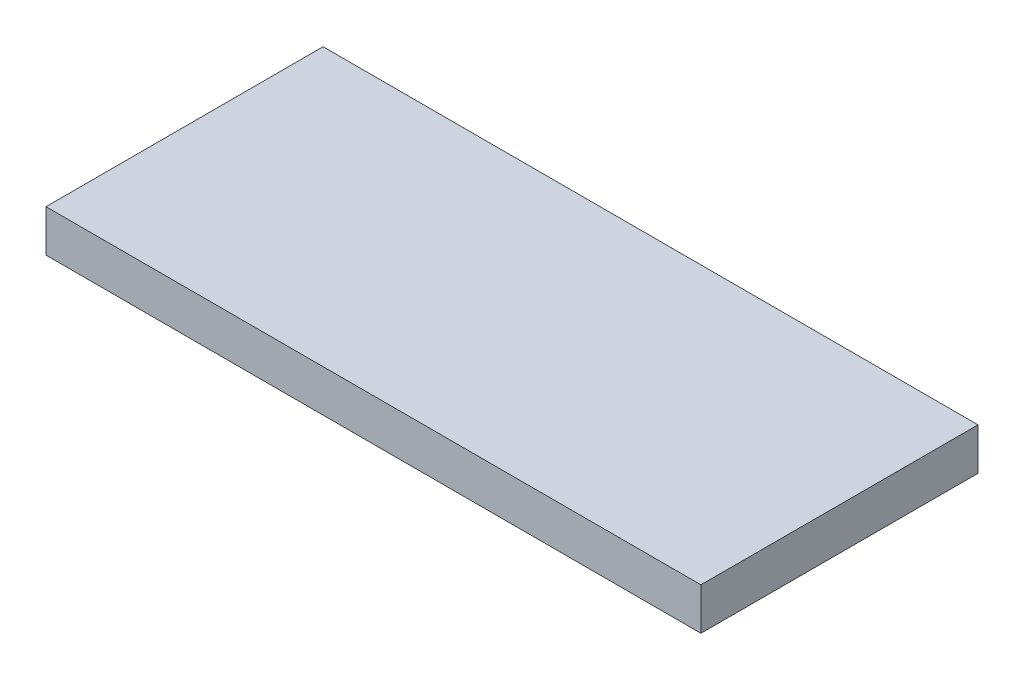
SolidWorks part; units mm, degrees
ref_plane "Спереди" through (0, 0, 0) normal (0, 0, 1) x (1, 0, 0)
ref_plane "Сверху" through (0, 0, 0) normal (0, 1, 0) x (1, 0, 0)
ref_plane "Справа" through (0, 0, 0) normal (1, 0, 0) x (0, 0, -1)
sketch "Эскиз1" plane through (0, 0, 0) normal (0, 1, 0) x (1, 0, 0)
  line L1 (0, 0) -> (78, 0)
  line L2 (0, 0) -> (0, 33)
  line L3 (0, 33) -> (78, 33)
  line L4 (78, 0) -> (78, 33)
extrude "Бобышка-Вытянуть1" add sketch "Эскиз1" along normal blind 5
